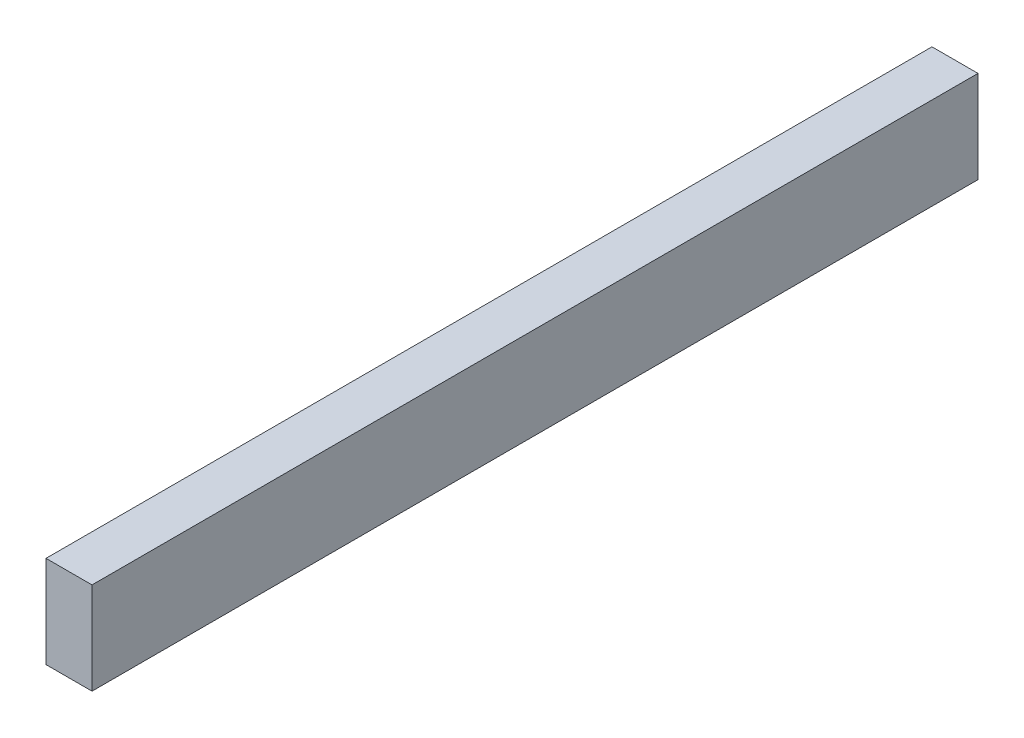
SolidWorks part; units mm, degrees
ref_plane "Front Plane" through (0, 0, 0) normal (0, 0, 1) x (1, 0, 0)
ref_plane "Top Plane" through (0, 0, 0) normal (0, 1, 0) x (1, 0, 0)
ref_plane "Right Plane" through (0, 0, 0) normal (1, 0, 0) x (0, 0, -1)
sketch "Sketch1" plane through (0, 0, 0) normal (0, 0, 1) x (1, 0, 0)
  line L1 (0, 0) -> (19.05, 0)
  line L2 (0, 0) -> (0, 38.1)
  line L3 (0, 38.1) -> (19.05, 38.1)
  line L4 (19.05, 0) -> (19.05, 38.1)
  dimension "D1" = 38.1
  dimension "D2" = 19.05
extrude "Boss-Extrude1" add sketch "Sketch1" along normal blind 366.7125
